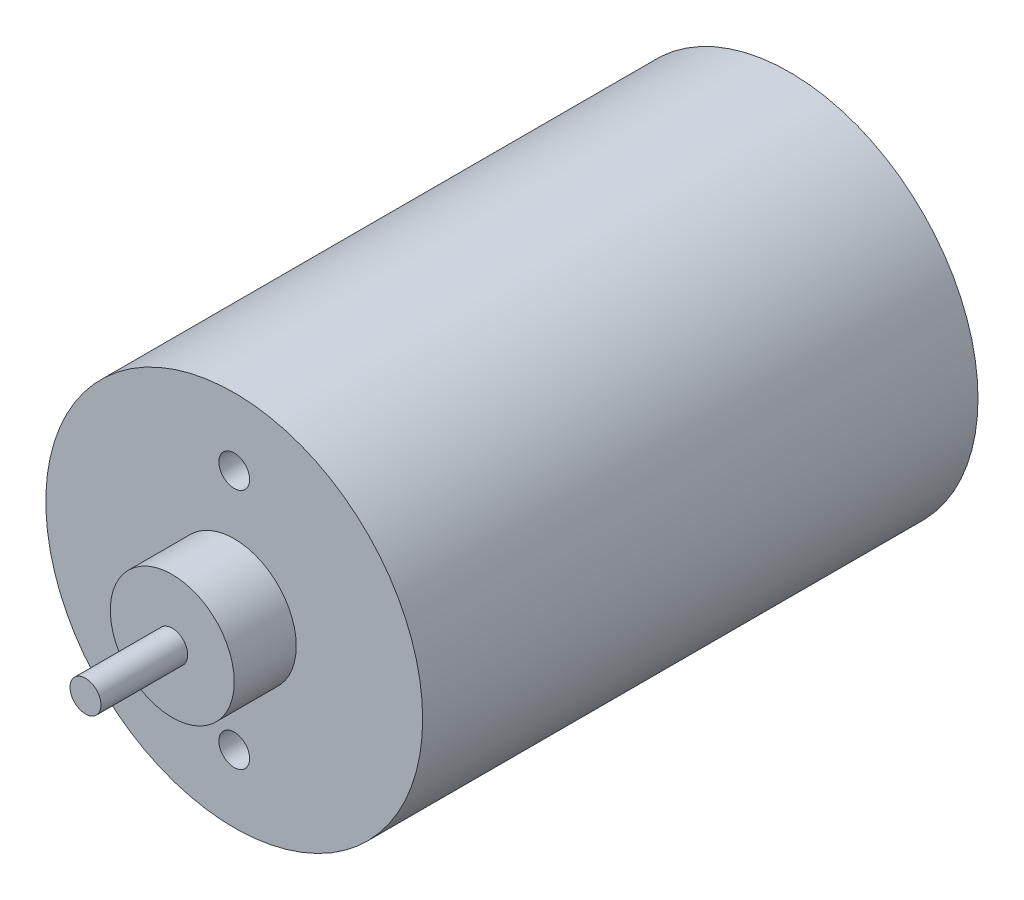
SolidWorks part; units mm, degrees
ref_plane "Front Plane" through (0, 0, 0) normal (0, 0, 1) x (1, 0, 0)
ref_plane "Top Plane" through (0, 0, 0) normal (0, 1, 0) x (1, 0, 0)
ref_plane "Right Plane" through (0, 0, 0) normal (1, 0, 0) x (0, 0, -1)
sketch "Sketch1" plane through (0, 0, 0) normal (0, 0, 1) x (1, 0, 0)
  circle A0 centre (0, 0) radius 19.304
  dimension "D1" = 38.608
extrude "Boss-Extrude1" add sketch "Sketch1" along normal blind 56.896
sketch "Sketch2" plane through (0, 0, 56.896) normal (0, 0, 1) x (1, 0, 0)
  circle A0 centre (0, 0) radius 6.35
  dimension "D1" = 12.7
extrude "Boss-Extrude2" add sketch "Sketch2" along normal blind 6.35
sketch "Sketch3" plane through (0, 0, 56.896) normal (0, 0, 1) x (1, 0, 0)
  line L0 (0, 12.3825) -> (0, -12.3825) construction
  circle A0 centre (0, 12.3825) radius 1.575
  circle A1 centre (0, -12.3825) radius 1.575
  point P4 (0, 0)
  dimension "D1" = 3.15
  dimension "D2" = 24.765
extrude "Cut-Extrude1" cut sketch "Sketch3" against normal blind 3.175
sketch "Sketch4" plane through (0, 0, 63.246) normal (0, 0, 1) x (1, 0, 0)
  circle A0 centre (0, 0) radius 1.5875
  dimension "D1" = 3.175
extrude "Boss-Extrude3" add sketch "Sketch4" along normal blind 8.89
